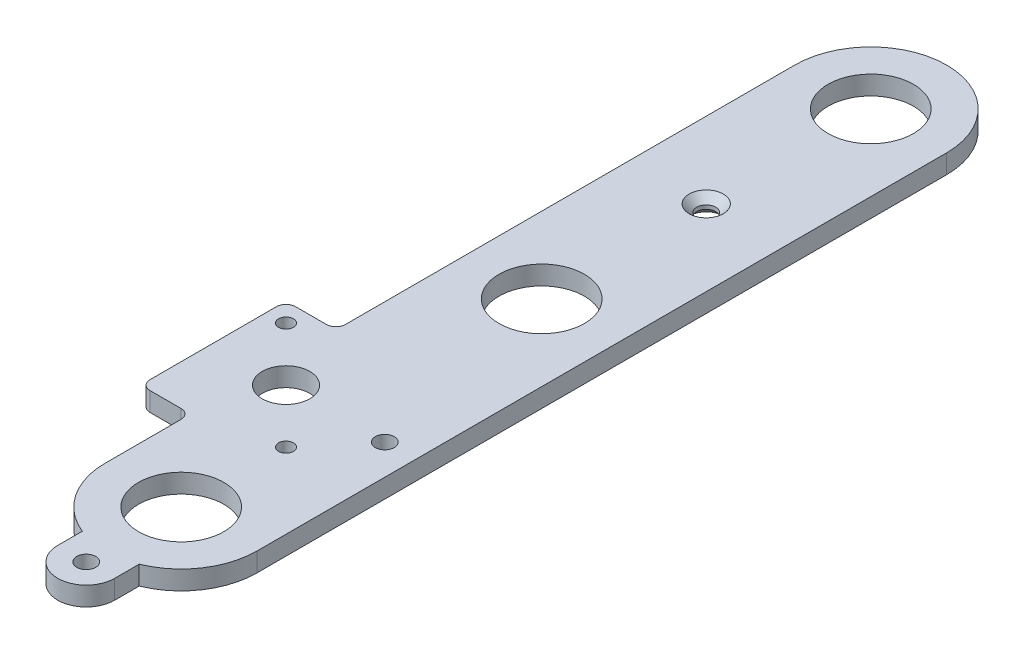
SolidWorks part; units mm, degrees
material "Acrylic (Medium-high impact)"
ref_plane "Front Plane" through (0, 0, 0) normal (0, 0, 1) x (1, 0, 0)
ref_plane "Top Plane" through (0, 0, 0) normal (0, 1, 0) x (1, 0, 0)
ref_plane "Right Plane" through (0, 0, 0) normal (1, 0, 0) x (0, 0, -1)
sketch "Sketch1" plane through (0, 0, 0) normal (0, 1, 0) x (1, 0, 0)
  line L0 (-352.425, 406.4) -> (-352.425, 488.95) construction
  line L1 (-352.425, -406.4) -> (352.425, -406.4) construction
  line L2 (-352.425, -406.4) -> (-352.425, 406.4) construction
  line L3 (-352.425, 406.4) -> (352.425, 406.4) construction
  line L4 (352.425, -406.4) -> (352.425, 406.4) construction
  line L5 (-352.425, -406.4) -> (352.425, 406.4) construction
  line L6 (-352.425, 406.4) -> (352.425, -406.4) construction
  line L7 (-434.975, -488.95) -> (434.975, -488.95) construction
  line L8 (-434.975, -488.95) -> (-434.975, 488.95) construction
  line L9 (-434.975, 488.95) -> (434.975, 488.95) construction
  line L10 (434.975, -488.95) -> (434.975, 488.95) construction
  line L11 (-434.975, -488.95) -> (434.975, 488.95) construction
  line L12 (-434.975, 488.95) -> (434.975, -488.95) construction
  line L13 (352.425, 406.4) -> (352.425, 488.95) construction
  line L14 (200.025, 488.95) -> (200.025, 406.4) construction
  line L15 (-200.025, 488.95) -> (-200.025, 406.4) construction
  line L16 (-352.425, 447.675) -> (-200.025, 447.675) construction
  line L17 (0, 0) -> (0, 262.3775) construction
  line L18 (200.025, 447.675) -> (352.425, 447.675) construction
  line L19 (-575.6491, 254) -> (705.9623, 254) construction
  line L20 (-139.7, 342.9) -> (139.7, 342.9) construction
  line L21 (-139.7, 342.9) -> (-139.7, 673.1) construction
  line L22 (-139.7, 673.1) -> (139.7, 673.1) construction
  line L23 (139.7, 342.9) -> (139.7, 673.1) construction
  line L24 (-139.7, 342.9) -> (139.7, 673.1) construction
  line L25 (-139.7, 673.1) -> (139.7, 342.9) construction
  line L26 (-165.1, 342.9) -> (165.1, 342.9) construction
  line L27 (-165.1, 342.9) -> (-165.1, 622.3) construction
  line L28 (-165.1, 622.3) -> (165.1, 622.3) construction
  line L29 (165.1, 342.9) -> (165.1, 622.3) construction
  line L30 (-165.1, 342.9) -> (165.1, 622.3) construction
  line L31 (-165.1, 622.3) -> (165.1, 342.9) construction
  line L32 (-498.863, 292.1) -> (699.369, 292.1) construction
  line L33 (-233.4867, 576.3867) -> (0, 809.8733) construction
  line L34 (-233.4867, 576.3867) -> (0, 342.9) construction
  line L35 (0, 809.8733) -> (233.4867, 576.3867) construction
  line L36 (0, 342.9) -> (233.4867, 576.3867) construction
  line L37 (0, 342.9) -> (0, 809.8733) construction
  line L38 (-210.82, 548.0346) -> (-210.82, 438.0272)
  line L39 (-210.82, 438.0272) -> (-210.82, 317.5)
  line L40 (210.82, 548.0346) -> (210.82, 438.0272)
  line L41 (210.82, 438.0272) -> (210.82, 317.5)
  line L42 (-210.82, 317.5) -> (210.82, 317.5)
  line L43 (-160.02, 548.0346) -> (160.02, 548.0346) construction
  line L44 (-210.82, 317.5) -> (-241.4506, 434.07) construction
  line L45 (-241.4506, 434.07) -> (-269.4077, 540.4656) construction
  line L46 (210.82, 317.5) -> (241.4506, 434.07) construction
  line L47 (241.4506, 434.07) -> (269.4077, 540.4656) construction
  line L48 (-434.975, 488.95) -> (-269.4077, 540.4656) construction
  line L49 (269.4077, 540.4656) -> (434.975, 488.95) construction
  line L50 (-269.4077, 540.4656) -> (-233.4867, 576.3867) construction
  line L51 (-434.975, 273.05) -> (20.0901, 273.05) construction
  line L52 (-210.82, 304.8) -> (210.82, 304.8) construction
  line L53 (-210.82, 304.8) -> (-210.82, 330.2) construction
  line L54 (-210.82, 330.2) -> (210.82, 330.2) construction
  line L55 (210.82, 304.8) -> (210.82, 330.2) construction
  circle A0 centre (-210.82, 548.0346) radius 50.8
  circle A1 centre (210.82, 548.0346) radius 50.8
  circle A2 centre (210.82, 438.0272) radius 50.8
  circle A3 centre (-210.82, 438.0272) radius 50.8
  circle A4 centre (269.4077, 540.4656) radius 50.8 construction
  circle A5 centre (241.4506, 434.07) radius 50.8 construction
  circle A6 centre (-241.4506, 434.07) radius 50.8 construction
  circle A7 centre (-269.4077, 540.4656) radius 50.8 construction
  point P0 (0, 0)
  point P6 (0, 0)
  point P22 (0, 508)
  point P28 (0, 482.6)
  point P67 (0, 317.5)
  point P68 (210.82, 317.5)
  dimension "D10" = 101.6
  dimension "D1" = 812.8
  dimension "D2" = 704.85
  dimension "D3" = 82.55
  dimension "D4" = 82.55
  dimension "D5" = 152.4
  dimension "D6" = 279.4
  dimension "D7" = 330.2
  dimension "D8" = 152.4
  dimension "D9" = 38.1
  dimension "D11" = 320.04
  dimension "D12" = 25.4
  dimension "D13" = 25.4
  dimension "D14" = 110.0074
  dimension "D15" = 25.4
  dimension "D16" = 19.05
sketch "Sketch3" plane through (0, 0, 0) normal (0, 1, 0) x (1, 0, 0)
  line L0 (-249.7355, 346.0124) -> (-239.395, 346.0124)
  line L1 (-252.9105, 349.1874) -> (-252.9105, 391.4584)
  line L2 (-210.82, 548.0346) -> (-210.82, 317.5) construction
  line L3 (-185.42, 548.0346) -> (-185.42, 317.5)
  line L7 (-210.82, 370.3229) -> (-228.6, 370.3229) construction
  line L10 (-246.5605, 352.3624) -> (-210.6395, 388.2834) construction
  line L11 (-228.6, 370.3229) -> (-210.82, 438.0272) construction
  line L12 (-246.5605, 352.3624) -> (-210.6395, 352.3624) construction
  line L13 (-246.5605, 352.3624) -> (-246.5605, 388.2834) construction
  line L14 (-246.5605, 388.2834) -> (-210.6395, 388.2834) construction
  line L15 (-210.6395, 352.3624) -> (-210.6395, 388.2834) construction
  line L16 (-210.82, 548.0346) -> (-210.82, 438.0272)
  line L17 (-210.82, 438.0272) -> (-228.6, 370.3229)
  line L18 (-210.82, 370.3229) -> (210.82, 370.3229) construction
  line L19 (210.82, 370.3229) -> (228.6, 370.3229) construction
  line L20 (210.82, 438.0272) -> (210.82, 317.5) construction
  line L21 (210.82, 438.0272) -> (210.82, 317.5) construction
  line L22 (-236.22, 397.8084) -> (-236.22, 548.0346)
  line L24 (-249.7355, 394.6334) -> (-239.395, 394.6334)
  line L25 (-252.9105, 346.0124) -> (-252.9105, 394.6334) construction
  line L26 (-252.9105, 394.6334) -> (-210.6395, 394.6334) construction
  line L27 (-236.22, 342.8374) -> (-236.22, 317.5)
  line L28 (-252.9105, 346.0124) -> (-210.6395, 346.0124) construction
  line L32 (-210.82, 317.5) -> (-210.82, 285.75) construction
  line L34 (-220.345, 293.9536) -> (-220.345, 285.75)
  line L35 (-201.295, 293.9536) -> (-201.295, 285.75)
  line L37 (-220.345, 293.9536) -> (-201.295, 293.9536) construction
  circle A8 centre (-210.82, 548.0346) radius 14.2748
  circle A9 centre (-210.82, 438.0272) radius 14.2748
  circle A10 centre (-210.82, 317.5) radius 14.2748
  arc A11 (-185.42, 548.0346) -> (-236.22, 548.0346) centre (-210.82, 548.0346) ccw
  arc A12 (-236.22, 317.5) -> (-220.345, 293.9536) centre (-210.82, 317.5) ccw
  circle A13 centre (-228.6, 370.3229) radius 7.9375
  circle A14 centre (-228.6, 370.3229) radius 25.4 construction
  arc A19 (-239.395, 346.0124) -> (-236.22, 342.8374) centre (-239.395, 342.8374) cw
  arc A20 (-249.7355, 346.0124) -> (-252.9105, 349.1874) centre (-249.7355, 349.1874) cw
  arc A21 (-252.9105, 391.4584) -> (-249.7355, 394.6334) centre (-249.7355, 391.4584) cw
  arc A22 (-239.395, 394.6334) -> (-236.22, 397.8084) centre (-239.395, 397.8084) ccw
  circle A24 centre (-246.5605, 388.2834) radius 2.4892
  circle A25 centre (-210.6395, 352.3624) radius 2.4892
  circle A26 centre (-210.82, 285.75) radius 3.175
  arc A28 (-220.345, 285.75) -> (-201.295, 285.75) centre (-210.82, 285.75) ccw
  arc A29 (-201.295, 293.9536) -> (-185.42, 317.5) centre (-210.82, 317.5) ccw
  circle A30 centre (-210.82, 493.0309) radius 3.175
  circle A31 centre (-195.58, 370.3229) radius 3.175
  dimension "D1" = 28.5496
  dimension "D3" = 15.875
  dimension "D4" = 4.9784
  dimension "D7" = 50.8
  dimension "D9" = 10.16
  dimension "D12" = 3.175
  dimension "D17" = 6.35
  dimension "D8" = 6.35
  dimension "D2" = 50.8
  dimension "D5" = 457.2
  dimension "D6" = 70
  dimension "D15" = 31.75
  dimension "D16" = 19.05
  dimension "D11" = 6.35
extrude "Boss-Extrude1" add sketch "Sketch3" along normal blind 6.35
chamfer "Chamfer1" distance 2.54 angle 45 2 edges at (-210.82, 0, -489.8559) (-210.82, 6.35, -489.8559)
